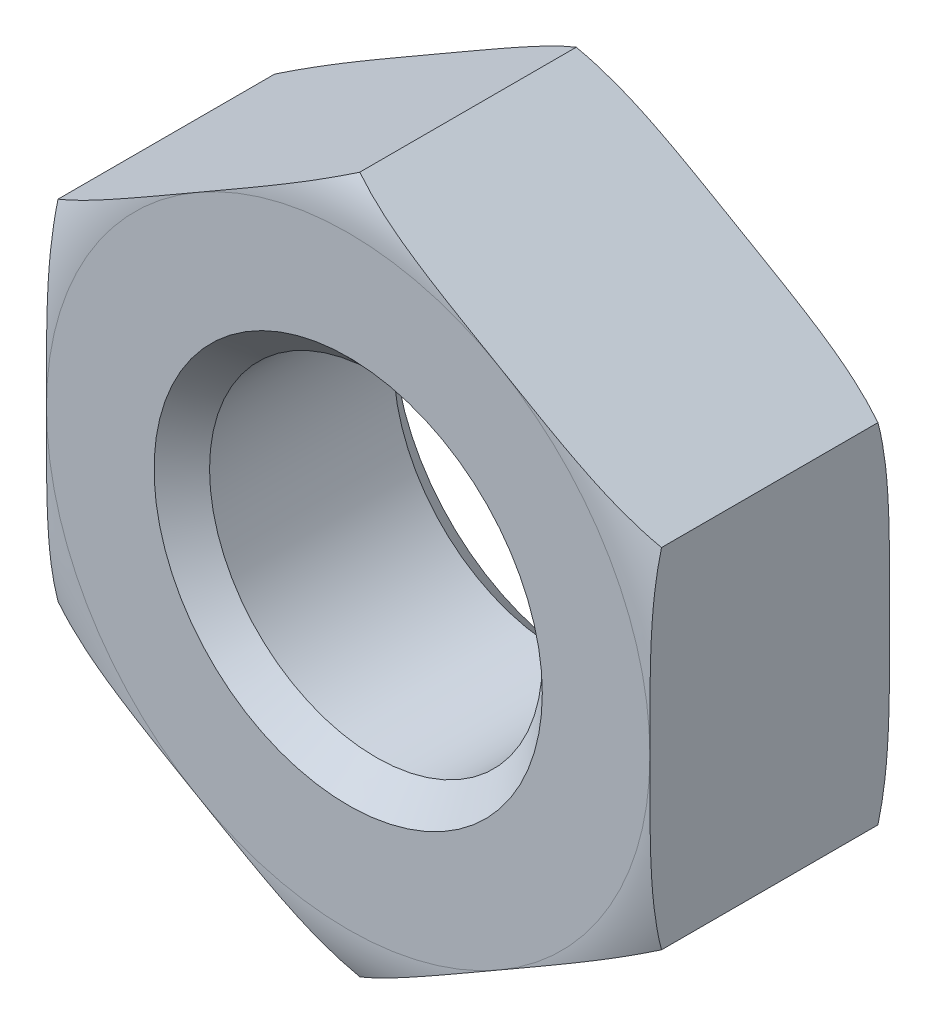
SolidWorks part; units mm, degrees
ref_plane "Front Plane" through (0, 0, 0) normal (0, 0, 1) x (1, 0, 0)
ref_plane "Top Plane" through (0, 0, 0) normal (0, 1, 0) x (1, 0, 0)
ref_plane "Right Plane" through (0, 0, 0) normal (1, 0, 0) x (0, 0, -1)
sketch "Sketch1" plane through (0, 0, 0) normal (0, 0, 1) x (1, 0, 0)
  line L1 (2.72, 1.5704) -> (0, 3.1408)
  line L2 (0, 3.1408) -> (-2.72, 1.5704)
  line L3 (-2.72, 1.5704) -> (-2.72, -1.5704)
  line L4 (-2.72, -1.5704) -> (0, -3.1408)
  line L5 (0, -3.1408) -> (2.72, -1.5704)
  line L6 (2.72, -1.5704) -> (2.72, 1.5704)
  circle A0 centre (0, 0) radius 2.72 construction
  circle A1 centre (0, 0) radius 1.5
  dimension "D1" = 3
  dimension "D2" = 5.44
extrude "Boss-Extrude1" add sketch "Sketch1" along normal blind 2.16
chamfer "Chamfer1" distance 0.25 angle 45 2 edges at (1.5, 0, 0) (1.5, 0, 2.16)
sketch "Sketch2" plane through (0, 0, 0) normal (0, 1, 0) x (1, 0, 0)
  line L0 (0, 0) -> (-2.72, 0) construction
  line L1 (-2.72, -2.16) -> (-2.72, 0) construction
  line L2 (0, -1.08) -> (-2.72, -1.08) construction
  line L3 (0, -2.16) -> (0, 0) construction
  line L4 (0, -1.08) -> (0, 1.437) construction
  line L5 (-3.5801, -0.6368) -> (-4.5008, -0.6368)
  line L6 (-4.5008, -0.6368) -> (-4.5008, 0.3612)
  line L7 (-4.5008, 0.3612) -> (-2.72, 0.3612)
  line L8 (-2.72, 0.3612) -> (-2.72, 0)
  line L9 (-2.72, -2.5212) -> (-2.72, -2.16)
  line L10 (-4.5008, -2.5212) -> (-2.72, -2.5212)
  line L11 (-4.5008, -1.5232) -> (-4.5008, -2.5212)
  line L12 (-3.5801, -1.5232) -> (-4.5008, -1.5232)
  arc A0 (-3.5801, -0.6368) -> (-2.72, 0) centre (-2.72, -0.8993) cw
  arc A1 (-3.5801, -1.5232) -> (-2.72, -2.16) centre (-2.72, -1.2607) ccw
  point P22 (-2.44, 0)
  point P23 (-2.44, 0)
  point P24 (-4, -0.3)
  point P25 (-4, -0.4405)
  point P26 (-3.3128, -0.4926)
revolve "Cut-Revolve1" cut sketch "Sketch2" angle 360 about L4
